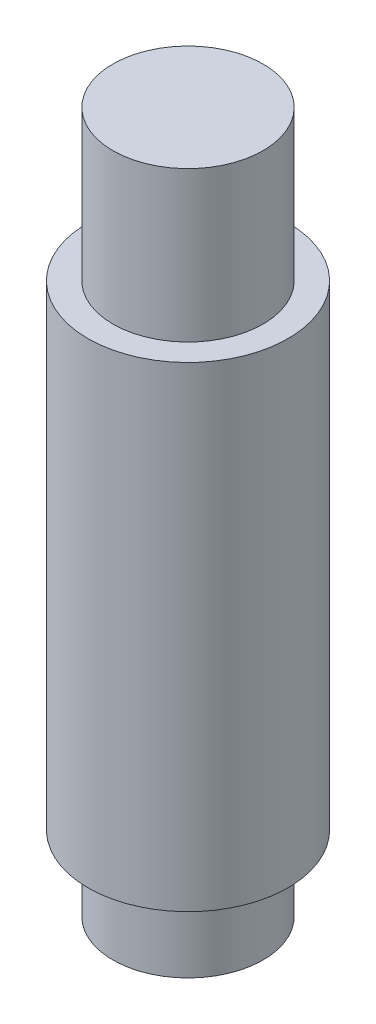
SolidWorks part; units mm, degrees
ref_plane "Front Plane" through (0, 0, 0) normal (0, 0, 1) x (1, 0, 0)
ref_plane "Top Plane" through (0, 0, 0) normal (0, 1, 0) x (1, 0, 0)
ref_plane "Right Plane" through (0, 0, 0) normal (1, 0, 0) x (0, 0, -1)
sketch "Sketch1" plane through (0, 0, 0) normal (0, 1, 0) x (1, 0, 0)
  circle A0 centre (0, 0) radius 20
  dimension "D1" = 40
extrude "Boss-Extrude1" add sketch "Sketch1" along normal mid plane 80
sketch "Sketch2" plane through (0, 40, 0) normal (0, 1, 0) x (1, 0, 0)
  circle A0 centre (0, 0) radius 15
  dimension "D1" = 30
extrude "Boss-Extrude2" add sketch "Sketch2" along normal blind 30
sketch "Sketch3" plane through (0, -40, 0) normal (0, -1, 0) x (1, 0, 0)
  circle A1 centre (0, 0) radius 15
  circle A2 centre (0, 0) radius 15
  dimension "D1" = 0
extrude "Boss-Extrude3" add sketch "Sketch3" along normal blind 30
sketch "Sketch4" plane through (0, -40, 0) normal (0, -1, 0) x (1, 0, 0)
  circle A0 centre (0, 0) radius 20 construction
  circle A1 centre (0, 0) radius 20
extrude "Boss-Extrude4" add sketch "Sketch4" along normal blind 15
